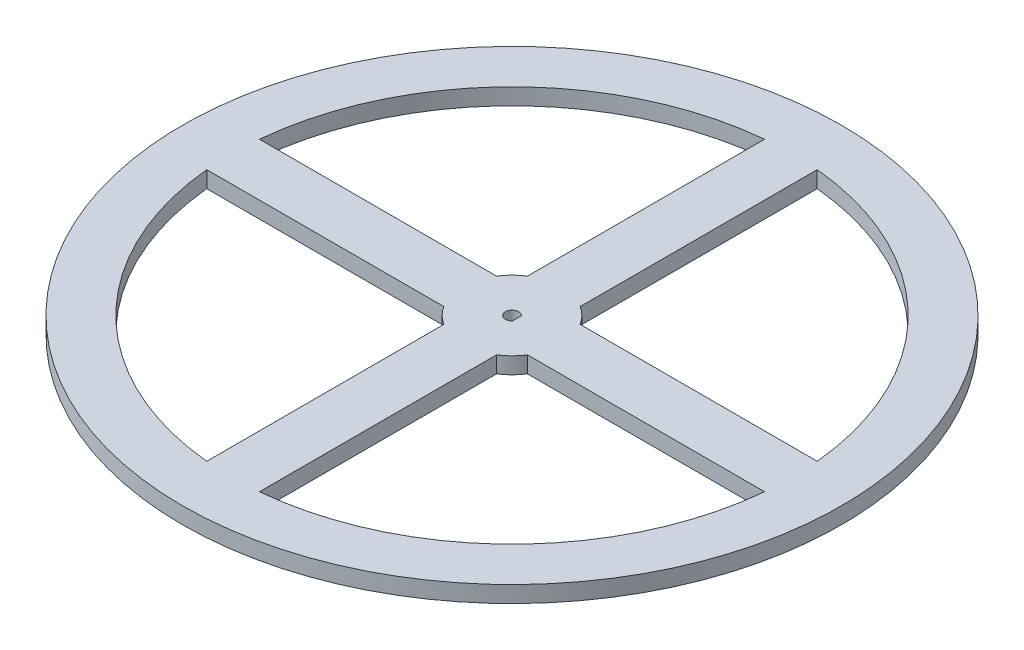
SolidWorks part; units mm, degrees
ref_plane "Front Plane" through (0, 0, 0) normal (0, 0, 1) x (1, 0, 0)
ref_plane "Top Plane" through (0, 0, 0) normal (0, 1, 0) x (1, 0, 0)
ref_plane "Right Plane" through (0, 0, 0) normal (1, 0, 0) x (0, 0, -1)
sketch "Sketch2" plane through (0, 0, 0) normal (0, 1, 0) x (1, 0, 0)
  line L2 (85, 8) -> (12.6886, 8)
  line L3 (85, -8) -> (12.6886, -8)
  line L4 (8, -85) -> (8, -12.6886)
  line L5 (-8, -85) -> (-8, -12.6886)
  line L7 (-8, 12.6886) -> (-8, 85)
  line L9 (-12.6886, 8) -> (-85, 8)
  line L14 (-12.6886, -8) -> (-85, -8)
  line L21 (8, 12.6886) -> (8, 85)
  arc A0 (12.6886, 8) -> (8, 12.6886) centre (0, 0) ccw
  arc A1 (8, -84.6227) -> (84.6227, -8) centre (0, 0) ccw
  circle A2 centre (0, 0) radius 100
  arc A3 (84.6227, 8) -> (8, 84.6227) centre (0, 0) ccw
  arc A4 (-8, 12.6886) -> (-12.6886, 8) centre (0, 0) ccw
  arc A5 (-12.6886, -8) -> (-8, -12.6886) centre (0, 0) ccw
  arc A6 (-8, 84.6227) -> (-84.6227, 8) centre (0, 0) ccw
  arc A7 (-84.6227, -8) -> (-8, -84.6227) centre (0, 0) ccw
  arc A8 (8, -12.6886) -> (12.6886, -8) centre (0, 0) ccw
extrude "Boss-Extrude1" add sketch "Sketch2" along normal blind 5
sketch "Sketch3" plane through (0, 0, 0) normal (0, -1, 0) x (1, 0, 0)
  line L1 (1.5, 0) -> (1.5, -1.3229)
  line L2 (1.5, 0) -> (1.5, 1.3229)
  arc A0 (1.5, 1.3229) -> (1.5, -1.3229) centre (0, 0) ccw
  dimension "D1" = 4
extrude "Cut-Extrude2" cut sketch "Sketch3" against normal blind 5
